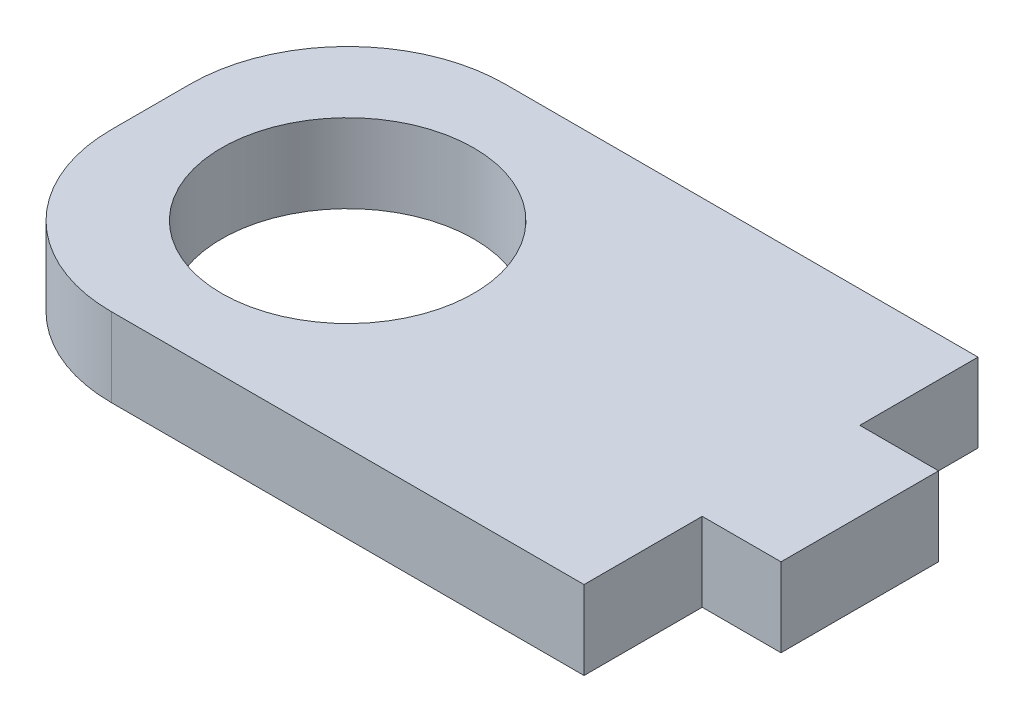
SolidWorks part; units mm, degrees
ref_plane "Plan de face" through (0, 0, 0) normal (0, 0, 1) x (1, 0, 0)
ref_plane "Plan de dessus" through (0, 0, 0) normal (0, 1, 0) x (1, 0, 0)
ref_plane "Plan de droite" through (0, 0, 0) normal (1, 0, 0) x (0, 0, -1)
sketch "Esquisse1" plane through (0, 0, 0) normal (0, 1, 0) x (1, 0, 0)
  line L0 (40, -7.5) -> (45, -7.5)
  line L1 (0, 0) -> (40, 0)
  line L2 (0, 0) -> (0, -25)
  line L3 (0, -25) -> (40, -25)
  line L4 (40, 0) -> (40, -7.5)
  line L5 (45, -7.5) -> (45, -17.5)
  line L6 (45, -17.5) -> (40, -17.5)
  line L7 (40, -17.5) -> (40, -25)
  circle A0 centre (12.5, -12.5) radius 8
  dimension "D2" = 16
  dimension "D1" = 5
  dimension "D3" = 27.5
  dimension "D4" = 25
  dimension "D5" = 10
  dimension "D6" = 7.5
  dimension "D7" = 40
  dimension "D8" = 12.5
extrude "Boss.-Extru.1" add sketch "Esquisse1" along normal blind 5
fillet "Congé1" radius 10 2 edges at (0, 2.5, 0) (0, 2.5, 25)
equation "\"D6@Esquisse1\"=(\"D4@Esquisse1\"-\"D5@Esquisse1\")/2"
equation "\"D8@Esquisse1\"=\"D4@Esquisse1\"/2"
